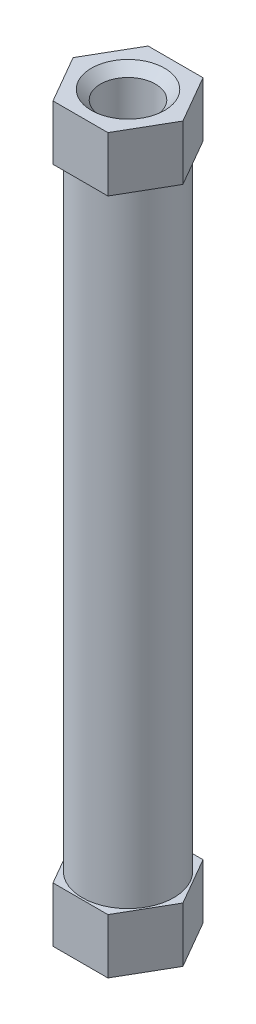
SolidWorks part; units mm, degrees
material "3003-O, Rod (SS)"
ref_plane "Front Plane" through (0, 0, 0) normal (0, 0, 1) x (1, 0, 0)
ref_plane "Top Plane" through (0, 0, 0) normal (0, 1, 0) x (1, 0, 0)
ref_plane "Right Plane" through (0, 0, 0) normal (1, 0, 0) x (0, 0, -1)
sketch "Sketch1" plane through (0, 0, 0) normal (0, 1, 0) x (1, 0, 0)
  line L1 (1.5, -2.5981) -> (3, 0)
  line L2 (3, 0) -> (1.5, 2.5981)
  line L3 (1.5, 2.5981) -> (-1.5, 2.5981)
  line L4 (-1.5, 2.5981) -> (-3, 0)
  line L5 (-3, 0) -> (-1.5, -2.5981)
  line L6 (-1.5, -2.5981) -> (1.5, -2.5981)
  circle A0 centre (0, 0) radius 2.5981 construction
  dimension "D1" = 6
extrude "Boss-Extrude1" add sketch "Sketch1" along normal blind 3
sketch "Sketch2" plane through (0, 3, 0) normal (0, 1, 0) x (1, 0, 0)
  circle A0 centre (0, 0) radius 2.5
  dimension "D1" = 5
extrude "Boss-Extrude2" add sketch "Sketch2" along normal blind 34
sketch "Sketch3" plane through (0, 37, 0) normal (0, 1, 0) x (1, 0, 0)
  line L1 (1.5, -2.5981) -> (3, 0)
  line L2 (3, 0) -> (1.5, 2.5981)
  line L3 (1.5, 2.5981) -> (-1.5, 2.5981)
  line L4 (-1.5, 2.5981) -> (-3, 0)
  line L5 (-3, 0) -> (-1.5, -2.5981)
  line L6 (-1.5, -2.5981) -> (1.5, -2.5981)
  circle A0 centre (0, 0) radius 2.5981 construction
  dimension "D1" = 6
extrude "Boss-Extrude3" add sketch "Sketch3" along normal blind 3
sketch "Sketch4" plane through (0, 40, 0) normal (0, 1, 0) x (1, 0, 0)
  circle A0 centre (0, 0) radius 1.5
  dimension "D1" = 3
extrude "Cut-Extrude1" cut sketch "Sketch4" against normal through all
chamfer "Chamfer1" distance 0.5 angle 45 2 edges at (0, 0, 1.5) (0, 40, 1.5)
